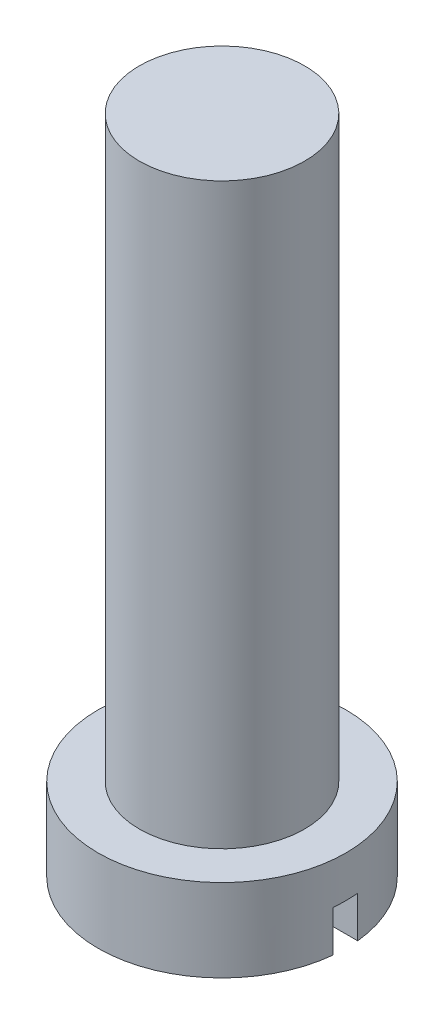
SolidWorks part; units mm, degrees
material "Alumina"
ref_plane "Front Plane" through (0, 0, 0) normal (0, 0, 1) x (1, 0, 0)
ref_plane "Top Plane" through (0, 0, 0) normal (0, 1, 0) x (1, 0, 0)
ref_plane "Right Plane" through (0, 0, 0) normal (1, 0, 0) x (0, 0, -1)
sketch "Sketch1" plane through (0, 0, 0) normal (0, 1, 0) x (1, 0, 0)
  circle A0 centre (0, 0) radius 3
  dimension "D1" = 6
extrude "Boss-Extrude1" add sketch "Sketch1" along normal blind 2
sketch "Sketch2" plane through (0, 2, 0) normal (0, 1, 0) x (1, 0, 0)
  circle A0 centre (0, 0) radius 2
  dimension "D1" = 4
extrude "Boss-Extrude2" add sketch "Sketch2" along normal blind 14
sketch "Sketch3" plane through (0, 0, 0) normal (0, -1, 0) x (1, 0, 0)
  line L3 (0, 0.3) -> (3.3447, 0.3)
  line L4 (3.3447, 0) -> (3.3447, 0.3)
  line L7 (0, 0.3) -> (-3.5082, 0.3)
  line L8 (-3.5082, 0) -> (-3.5082, 0.3)
  line L11 (0, -0.3) -> (3.3447, -0.3)
  line L12 (3.3447, 0) -> (3.3447, -0.3)
  line L15 (0, -0.3) -> (-3.5082, -0.3)
  line L16 (-3.5082, 0) -> (-3.5082, -0.3)
  dimension "D1" = 0.3
  dimension "D2" = 0.3
extrude "Cut-Extrude2" cut sketch "Sketch3" against normal blind 1
